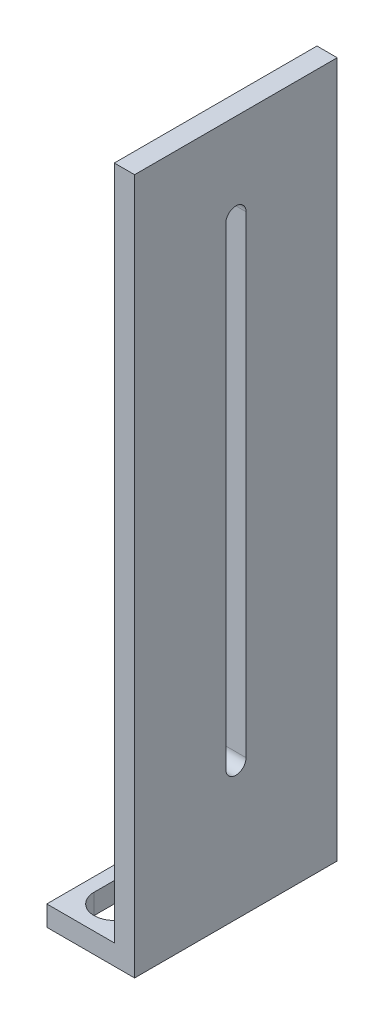
SolidWorks part; units mm, degrees
ref_plane "前视基准面" through (0, 0, 0) normal (0, 0, 1) x (1, 0, 0)
ref_plane "上视基准面" through (0, 0, 0) normal (0, 1, 0) x (1, 0, 0)
ref_plane "右视基准面" through (0, 0, 0) normal (1, 0, 0) x (0, 0, -1)
sketch "草图5" plane through (0, 0, 0) normal (0, 1, 0) x (1, 0, 0)
  line L0 (0, 0) -> (0, -30)
  line L1 (0, -30) -> (10, -30)
  line L2 (10, -30) -> (10, 0)
  line L3 (10, 0) -> (0, 0)
  line L4 (5, 0) -> (5, -30) construction
  line L5 (5, -5) -> (5, -25) construction
  line L6 (8, -5) -> (8, -25)
  line L7 (2, -5) -> (2, -25)
  arc A0 (8, -5) -> (2, -5) centre (5, -5) ccw
  arc A1 (2, -25) -> (8, -25) centre (5, -25) ccw
  point P7 (5, -5)
  point P8 (5, -25)
  point P9 (5, -15)
extrude "凸台-拉伸5" add sketch "草图5" along normal blind 3
sketch "草图6" plane through (10, 0, 0) normal (1, 0, 0) x (0, 0, -1)
  line L0 (-30, 3) -> (-30, 103)
  line L1 (-30, 103) -> (0, 103)
  line L2 (0, 103) -> (0, 3)
  line L3 (0, 3) -> (-30, 3)
  line L4 (-30, 3) -> (-30, 0)
  line L5 (-30, 0) -> (0, 0)
  line L6 (0, 0) -> (0, 3)
  line M1 (-30, 0) -> (0, 0)
  line M2 (0, 0) -> (0, 3)
  line M3 (0, 3) -> (-30, 3)
  line M4 (-30, 3) -> (-30, 0)
extrude "凸台-拉伸6" add sketch "草图6" along normal blind 3 contours L2 L1 L0 M3 | M4 M1 M2 M3
sketch "草图7" plane through (10, 0, 0) normal (-1, 0, 0) x (0, 0, 1)
  line L0 (15, 103) -> (15, 3) construction
  line L1 (30, 103) -> (0, 103) construction
  line L2 (30, 3) -> (0, 3) construction
  line L3 (15, 90) -> (15, 20) construction
  line L4 (16.5, 90) -> (16.5, 20)
  line L5 (13.5, 90) -> (13.5, 20)
  arc A0 (16.5, 90) -> (13.5, 90) centre (15, 90) ccw
  arc A1 (13.5, 20) -> (16.5, 20) centre (15, 20) ccw
  point P6 (13.5, 87.5543)
  point P7 (15, 20)
  point P8 (15, 55)
  point P18 (15, 90)
extrude "切除-拉伸2" cut sketch "草图7" against normal blind 3
